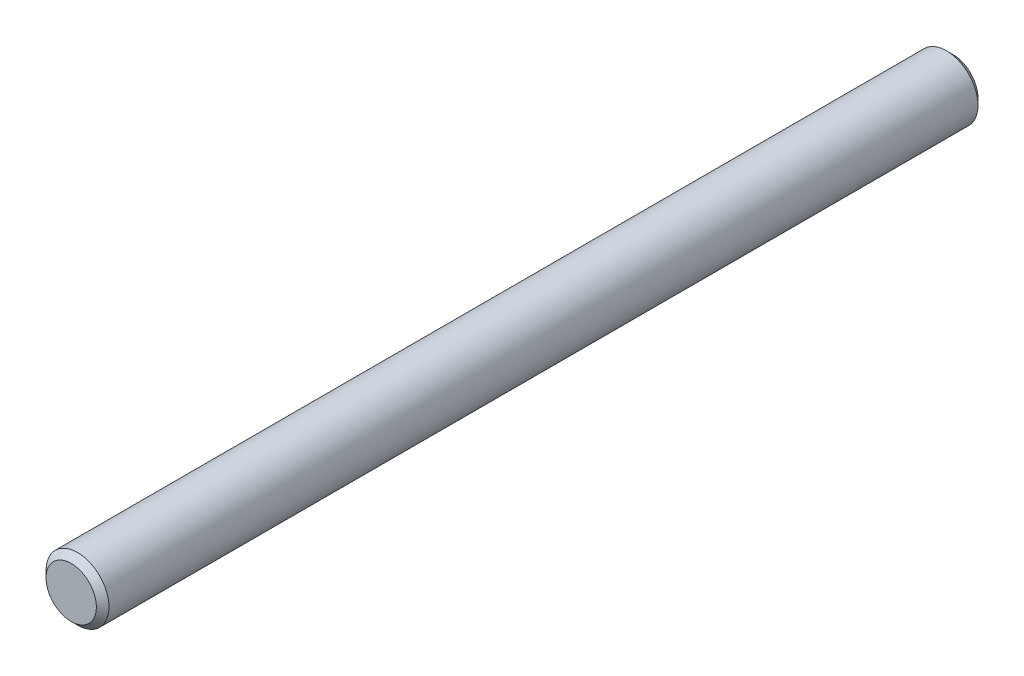
SolidWorks part; units mm, degrees
ref_plane "前视基准面" through (0, 0, 0) normal (0, 0, 1) x (1, 0, 0)
ref_plane "上视基准面" through (0, 0, 0) normal (0, 1, 0) x (1, 0, 0)
ref_plane "右视基准面" through (0, 0, 0) normal (1, 0, 0) x (0, 0, -1)
sketch "草图1" plane through (0, 0, 0) normal (0, 0, 1) x (1, 0, 0)
  circle A0 centre (0, 0) radius 2.5
extrude "凸台-拉伸1" add sketch "草图1" along normal blind 70
chamfer "倒角1" distance 0.5 angle 45 2 edges at (2.5, 0, 70) (2.5, 0, 0)
